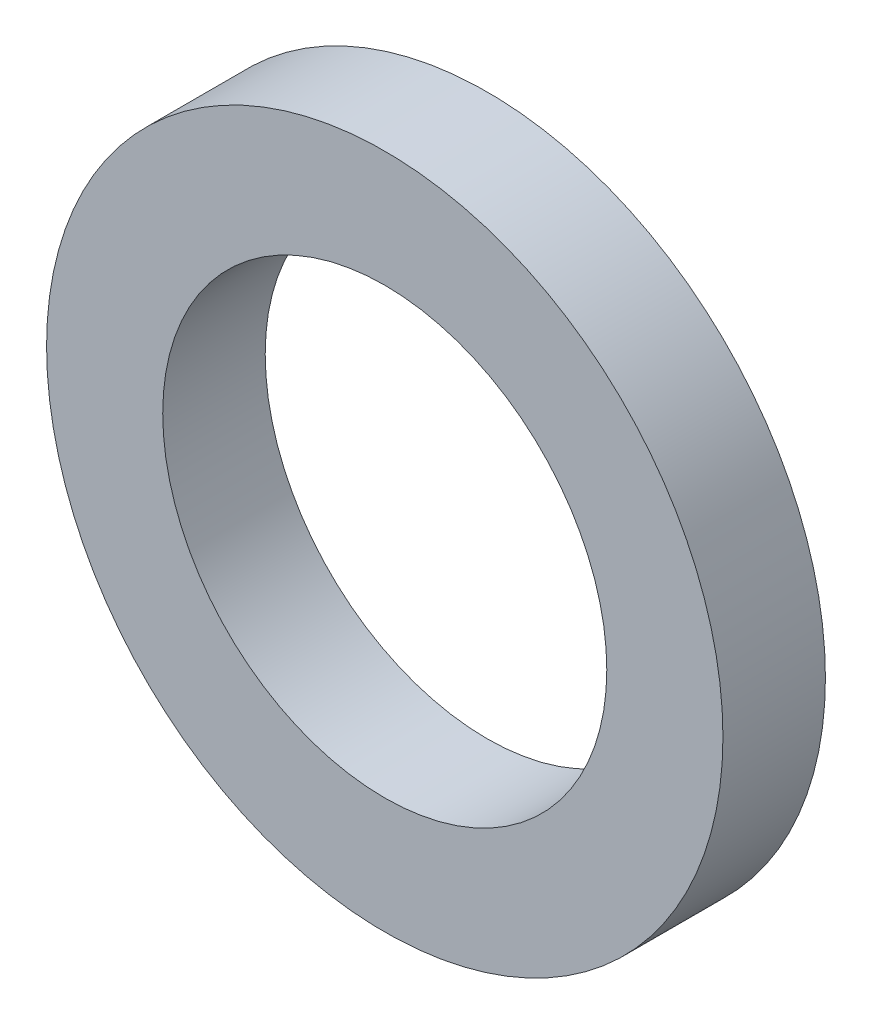
SolidWorks part; units mm, degrees
ref_plane "Front Plane" through (0, 0, 0) normal (0, 0, 1) x (1, 0, 0)
ref_plane "Top Plane" through (0, 0, 0) normal (0, 1, 0) x (1, 0, 0)
ref_plane "Right Plane" through (0, 0, 0) normal (1, 0, 0) x (0, 0, -1)
sketch "Sketch1" plane through (0, 0, 0) normal (0, 0, 1) x (1, 0, 0)
  circle A0 centre (0, 0) radius 4.95
  circle A1 centre (0, 0) radius 3.25
  dimension "ID" = 6.5
  dimension "OD" = 9.9
extrude "Boss-Extrude1" add sketch "Sketch1" along normal blind 1.5
